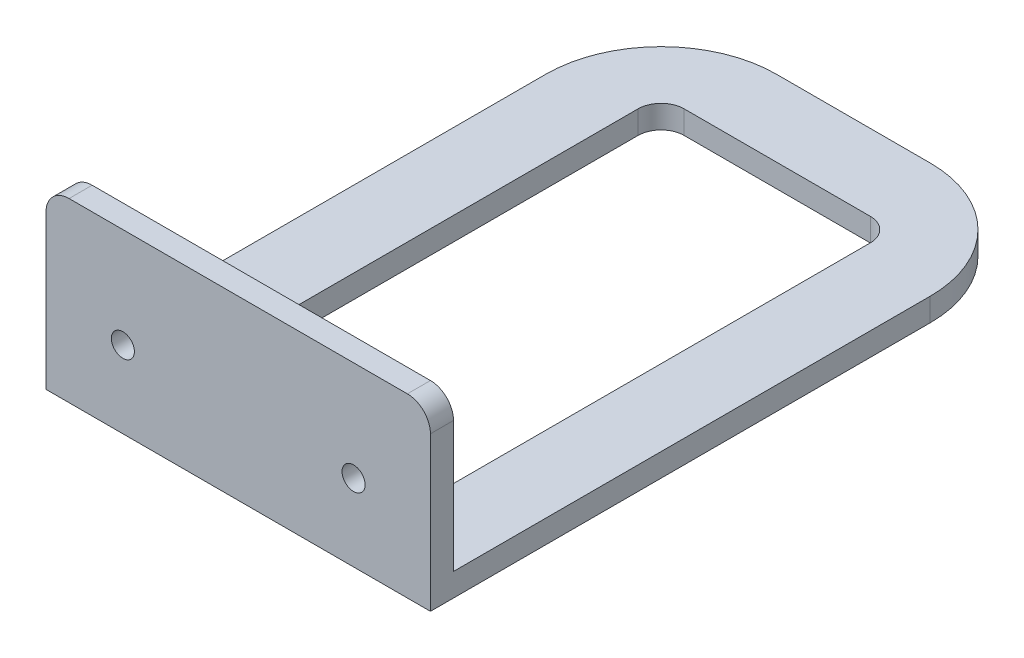
SolidWorks part; units mm, degrees
ref_plane "Front Plane" through (0, 0, 0) normal (0, 0, 1) x (1, 0, 0)
ref_plane "Top Plane" through (0, 0, 0) normal (0, 1, 0) x (1, 0, 0)
ref_plane "Right Plane" through (0, 0, 0) normal (1, 0, 0) x (0, 0, -1)
sketch "Sketch1" plane through (0, 0, 0) normal (0, 1, 0) x (1, 0, 0)
  line L1 (-25, 40) -> (25, 40)
  line L2 (-25, 40) -> (-25, -40)
  line L3 (-25, -40) -> (25, -40)
  line L4 (25, 40) -> (25, -40)
  line L5 (-25, 40) -> (25, -40) construction
  line L6 (-25, -40) -> (25, 40) construction
  point P0 (0, 0)
extrude "Boss-Extrude1" add sketch "Sketch1" along normal blind 3
sketch "Sketch2" plane through (0, 3, 0) normal (0, 1, 0) x (1, 0, 0)
  line L0 (25, -40) -> (25, 40) construction
  line L1 (-25, -40) -> (25, -40)
  line L2 (-25, -40) -> (-25, -37)
  line L3 (-25, -37) -> (25, -37)
  line L4 (25, -40) -> (25, -37)
extrude "Boss-Extrude2" add sketch "Sketch2" along normal blind 20
fillet "Fillet1" radius 3 2 edges at (-25, 23, 38.5) (25, 23, 38.5)
fillet "Fillet2" radius 15 2 edges at (25, 1.5, -40) (-25, 1.5, -40)
sketch "Sketch3" plane through (0, 3, 0) normal (0, 1, 0) x (1, 0, 0)
  line L1 (-12.1, 30.1) -> (12.1, 30.1)
  line L2 (-15.1, 27.1) -> (-15.1, -27.1)
  line L3 (-12.1, -30.1) -> (12.1, -30.1)
  line L4 (15.1, 27.1) -> (15.1, -27.1)
  line L5 (-15.1, 30.1) -> (15.1, -30.1) construction
  line L6 (-15.1, -30.1) -> (15.1, 30.1) construction
  arc A0 (12.1, -30.1) -> (15.1, -27.1) centre (12.1, -27.1) ccw
  arc A1 (-15.1, -27.1) -> (-12.1, -30.1) centre (-12.1, -27.1) ccw
  arc A2 (12.1, 30.1) -> (15.1, 27.1) centre (12.1, 27.1) cw
  arc A3 (-12.1, 30.1) -> (-15.1, 27.1) centre (-12.1, 27.1) ccw
  point P0 (0, 0)
  dimension "D1" = 3
  dimension "D2" = 30.2
  dimension "D3" = 60.2
extrude "Cut-Extrude1" cut sketch "Sketch3" against normal through all contours L2 A1 L3 A0 L4 A2 L1 A3
sketch "Sketch4" plane through (0, 0, 40) normal (0, 0, 1) x (1, 0, 0)
  line L1 (-15, 10) -> (15, 10)
  line L2 (-15, 10) -> (-15, -10)
  line L3 (-15, -10) -> (15, -10)
  line L4 (15, 10) -> (15, -10)
  line L5 (-15, 10) -> (15, -10) construction
  line L6 (-15, -10) -> (15, 10) construction
  circle A0 centre (-15, 10) radius 1.5
  circle A1 centre (15, 10) radius 1.5
  point P0 (0, 0)
extrude "Cut-Extrude2" cut sketch "Sketch4" against normal through all contours L1 A0 L2 | L2 A0 L1 | L1 A1 L4 | L4 A1 L1
